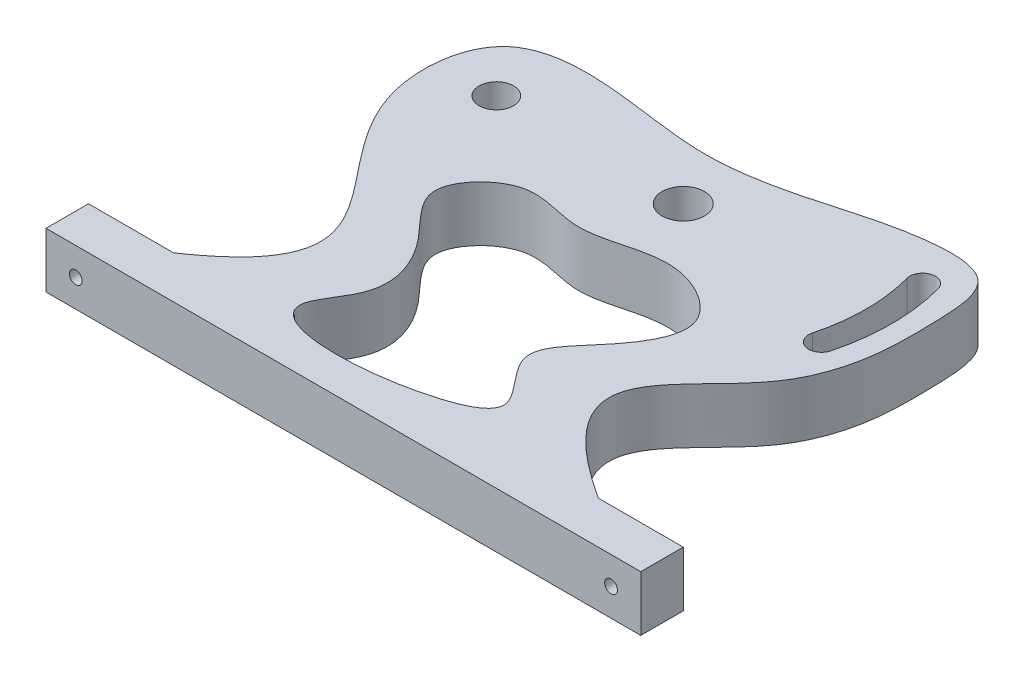
SolidWorks part; units mm, degrees
ref_plane "Спереди" through (0, 0, 0) normal (0, 0, 1) x (1, 0, 0)
ref_plane "Сверху" through (0, 0, 0) normal (0, 1, 0) x (1, 0, 0)
ref_plane "Справа" through (0, 0, 0) normal (1, 0, 0) x (0, 0, -1)
sketch "Эскиз1" plane through (0, 0, 0) normal (0, 1, 0) x (1, 0, 0)
  line L0 (-39.1725, -43.9447) -> (100.8275, -43.9447)
  line L1 (30.8275, 36.0553) -> (30.8275, -103.29) construction
  line L2 (-39.1725, -43.9447) -> (-39.1725, -33.9447)
  line L3 (-39.1725, -33.9447) -> (-19.1725, -33.9447)
  line L4 (100.8275, -33.9447) -> (80.8275, -33.9447)
  line L5 (100.8275, -43.9447) -> (100.8275, -33.9447)
  line L6 (30.8275, 36.0553) -> (86.7699, 51.045) construction
  line L7 (30.8275, 36.0553) -> (89.8519, 20.2397) construction
  line L8 (30.8275, 36.0553) -> (100.8275, 36.0553) construction
  arc A0 (72.3623, 24.9261) -> (72.3623, 47.1845) centre (30.8275, 36.0553) ccw
  arc A1 (78.1578, 23.3732) -> (78.1578, 48.7374) centre (30.8275, 36.0553) ccw
  circle A2 centre (30.8275, 36.0553) radius 5
  circle A3 centre (-13.1725, 36.0553) radius 4.0644
  arc A4 (78.1578, 48.7374) -> (72.3623, 47.1845) centre (75.2601, 47.961) ccw
  arc A5 (72.3623, 24.9261) -> (78.1578, 23.3732) centre (75.2601, 24.1496) ccw
  circle A7 centre (30.8275, 36.0553) radius 43 construction
  circle A8 centre (30.8275, 36.0553) radius 49 construction
  spline S0 degree 3 poles (-19.1725, -33.9447) (15.4311, -10.54) (-31.2474, 4.1216) (-26.205, 51.9267) (2.0271, 51.7225) (22.5567, 47.2506) (45.3291, 51.6332) (61.8985, 57.4247) (83.888, 58.4073) (84.6803, 39.8195) (84.7178, 26.0687) (75.2205, -1.518) (44.445, -10.4411) (80.8275, -33.9447) knots 0 0 0 0 0.233238 0.310066 0.386429 0.471525 0.535672 0.612571 0.667147 0.712512 0.770252 0.815619 1 1 1 1
  spline S1 degree 3 poles (32.2374, -37.0458) (-1.9597, -36.6062) (14.9382, -17.1095) (8.9267, -2.4298) (-5.6284, 8.9393) (8.2878, 23.8328) (24.984, 15.8344) (40.811, 26.0172) (61.288, 13.7925) (51.3205, -1.6484) (38.7024, -13.8715) (56.4581, -26.8922) (32.2374, -37.0458) (-1.9597, -36.6062) (14.9382, -17.1095) knots -0.305935 -0.234825 -0.167869 0 0.053473 0.141845 0.214493 0.285603 0.356448 0.464566 0.54201 0.62731 0.694065 0.765175 0.832131 1 1.053473 1.141845 1.214493 only from (6.5188, -28.6114) to (6.5188, -28.6114)
  point P1 (79.8275, 36.0553)
  point P18 (30.8275, -43.9447)
  point P19 (71.9486, 48.6273)
  dimension "D2" = 86
  dimension "D3" = 6
  dimension "D11" = 10
  dimension "D4" = 30
  dimension "D5" = 15
  dimension "D6" = 54
  dimension "D7" = 80
  dimension "D8" = 70
  dimension "D9" = 10
  dimension "D10" = 20
  dimension "D12" = 44
  dimension "D13" = 54
  dimension "D14" = 54
extrude "Бобышка-Вытянуть1" add sketch "Эскиз1" along normal blind 13
sketch "Эскиз2" plane through (0, 0, 33.9447) normal (0, 0, -1) x (-1, 0, 0)
  line L0 (-100.8275, 6.5) -> (-81.8507, 6.5) construction
  line L1 (-100.8275, 13) -> (-100.8275, 0) construction
  line L2 (39.1725, 13) -> (39.1725, 0) construction
  circle A0 centre (-93.8275, 6.5) radius 1.5
  circle A1 centre (32.1725, 6.5) radius 1.5
  dimension "D1" = 7
  dimension "D2" = 3
  dimension "D3" = 3
  dimension "D4" = 7
extrude "Вырез-Вытянуть1" cut sketch "Эскиз2" against normal through all
